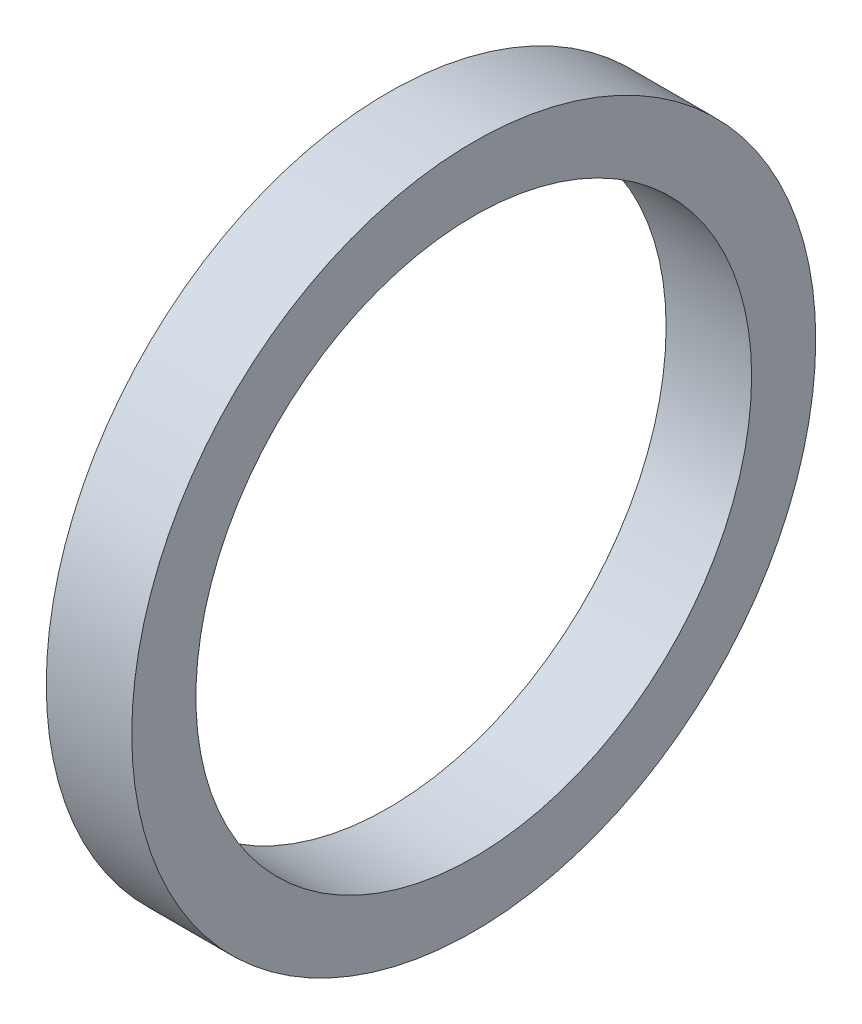
SolidWorks part; units mm, degrees
ref_plane "Front Plane" through (0, 0, 0) normal (0, 0, 1) x (1, 0, 0)
ref_plane "Top Plane" through (0, 0, 0) normal (0, 1, 0) x (1, 0, 0)
ref_plane "Right Plane" through (0, 0, 0) normal (1, 0, 0) x (0, 0, -1)
sketch "Sketch1" plane through (0, 0, 0) normal (1, 0, 0) x (0, 0, -1)
  circle A0 centre (0, 0) radius 40
  circle A1 centre (0, 0) radius 32.5
  dimension "D1" = 80
  dimension "D2" = 7.5
extrude "Boss-Extrude1" add sketch "Sketch1" along normal blind 10
